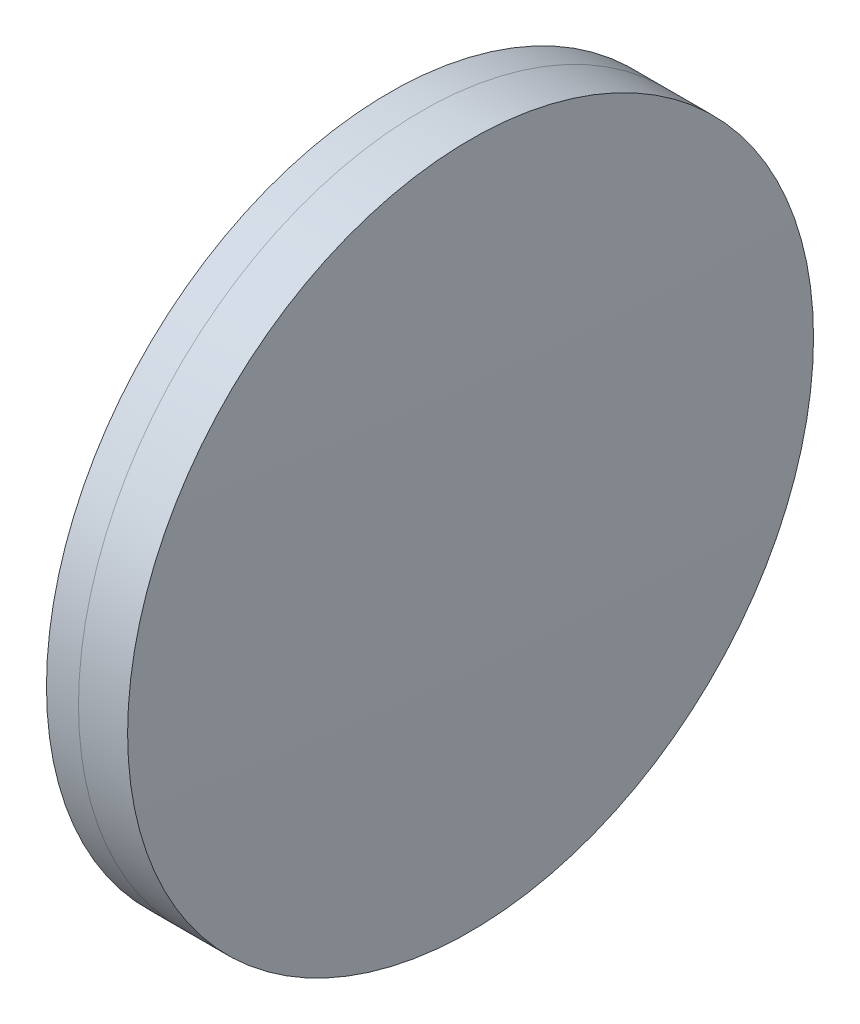
SolidWorks part; units mm, degrees
ref_plane "前视基准面" through (0, 0, 0) normal (0, 0, 1) x (1, 0, 0)
ref_plane "上视基准面" through (0, 0, 0) normal (0, 1, 0) x (1, 0, 0)
ref_plane "右视基准面" through (0, 0, 0) normal (1, 0, 0) x (0, 0, -1)
sketch "草图1" plane through (0, 0, 0) normal (0, 1, 0) x (1, 0, 0)
  line L0 (124.5233, 0) -> (395.1269, 0) construction
  line L1 (310.5066, -20) -> (312.3748, -20)
  line L2 (310.5066, 20) -> (312.3748, 20)
  arc A0 (312.3748, -20) -> (312.3748, 20) centre (151.2191, 0) ccw
  arc A1 (310.5066, 20) -> (310.5066, -20) centre (555.3311, 0) ccw
  point P10 (309.6911, 0)
  point P11 (313.6111, 0)
  dimension "D3" = 245.64
  dimension "D4" = 162.392
  dimension "D1" = 20
  dimension "D2" = 20
  dimension "D5" = 3.92
revolve "旋转1" add sketch "草图1" angle 360 about L0
sketch "草图2" plane through (0, 0, 0) normal (0, 1, 0) x (1, 0, 0)
  line L0 (-0.5519, 0) -> (409.4962, 0) construction
  line L2 (312.3748, 20) -> (315.2377, 20)
  line L3 (312.3748, -20) -> (315.2377, -20)
  arc A0 (315.2377, -20) -> (315.2377, 20) centre (-220.2049, 0) ccw
  arc A1 (312.3748, -20) -> (312.3748, 20) centre (151.2191, 0) ccw construction
  arc A2 (312.3748, -20) -> (312.3748, 20) centre (151.2191, 0) ccw
  point P4 (313.6111, 0)
  point P8 (315.6111, 0)
  dimension "D1" = 535.816
  dimension "D2" = 2
revolve "旋转3" add sketch "草图2" angle 360 about L0
